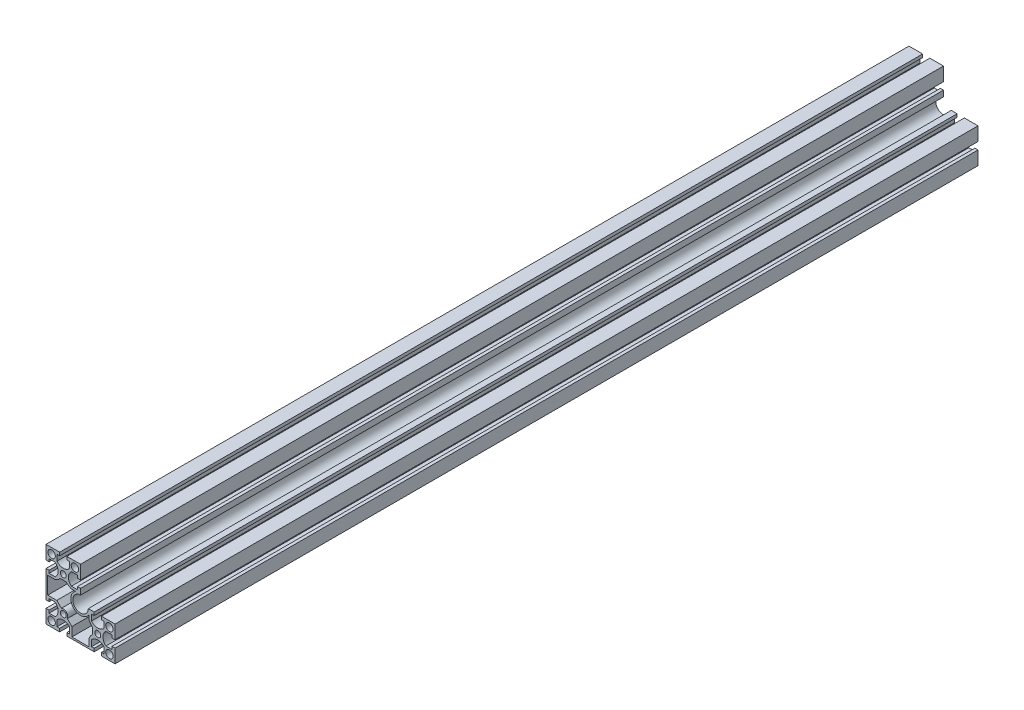
SolidWorks part; units mm, degrees
material "6063 T5"
ref_plane "Спереди" through (0, 0, 0) normal (0, 0, 1) x (1, 0, 0)
ref_plane "Сверху" through (0, 0, 0) normal (0, 1, 0) x (1, 0, 0)
ref_plane "Справа" through (0, 0, 0) normal (1, 0, 0) x (0, 0, -1)
sketch "Эскиз1" plane through (0, 0, 0) normal (0, 0, 1) x (1, 0, 0)
  line L0 (-19.9727, 74.2967) -> (60.0273, 74.2967) construction
  line L1 (0, 40) -> (0, 0) construction
  line L2 (0, 0) -> (40, 0) construction
  line L3 (-20, 47.3) -> (-20, 60)
  line L4 (-20, 60) -> (-7.3, 60)
  line L5 (7.3, 60) -> (20, 60)
  line L6 (20, 60) -> (20, 47.3)
  line L7 (0, 20) -> (-33.7669, 20) construction
  line L8 (-20, -7.3) -> (-20, -20)
  line L9 (-20, -20) -> (-7.3, -20)
  line L10 (-20, 32.7) -> (-20, 7.3)
  line L11 (0, 0) -> (36.7738, 36.7738) construction
  line L12 (32.7, -20) -> (7.3, -20)
  line L13 (47.3, -20) -> (60, -20)
  line L14 (60, -20) -> (60, -7.3)
  line L15 (60, 7.3) -> (60, 20)
  line L16 (60, 20) -> (47.3, 20)
  line L17 (20, 32.7) -> (20, 29)
  line L18 (29, 20) -> (32.7, 20)
  line L19 (-2.208, 4.708) -> (-7.5, 10)
  line L20 (-7.5, 10) -> (-18, 10)
  line L21 (-18, 10) -> (-18, 30)
  line L22 (-18, 30) -> (-9, 30)
  line L23 (-9, 30) -> (-5.451, 32.049)
  line L24 (-5.451, 32.049) -> (-3.5, 34)
  line L25 (-3.5, 34) -> (3.5, 34)
  line L26 (3.5, 34) -> (5.451, 32.049)
  line L27 (5.451, 32.049) -> (9, 30)
  line L28 (9, 30) -> (14.7379, 30)
  line L29 (30, 9) -> (30, 14.7379)
  line L30 (32.049, 5.451) -> (30, 9)
  line L31 (34, 3.5) -> (32.049, 5.451)
  line L32 (34, -3.5) -> (34, 3.5)
  line L33 (32.049, -5.451) -> (34, -3.5)
  line L34 (30, -9) -> (32.049, -5.451)
  line L35 (30, -18) -> (30, -9)
  line L36 (10, -18) -> (30, -18)
  line L37 (10, -7.5) -> (10, -18)
  line L38 (4.708, -2.208) -> (10, -7.5)
  circle A0 centre (0, 40) radius 3.4
  circle A1 centre (-13.5, 53.5) radius 4.3
  circle A3 centre (13.5, 53.5) radius 4.3
  circle A4 centre (-13.5, -13.5) radius 4.3
  circle A5 centre (0, 0) radius 3.4
  circle A6 centre (40, 0) radius 3.4
  circle A7 centre (53.5, 13.5) radius 4.3
  circle A8 centre (53.5, -13.5) radius 4.3
  arc A9 (20, 29) -> (29, 20) centre (20, 20) ccw
  arc A10 (4.708, -2.208) -> (-2.208, 4.708) centre (0, 0) ccw
  arc A11 (14.7379, 30) -> (30, 14.7379) centre (20, 20) ccw
  point P7 (-20, 40)
  point P11 (0, 40)
  point P62 (0, 34)
  line B0 (-20, 47.3) -> (-20, 44.2)
  line B1 (-20, 44.2) -> (-16.4, 44.2)
  line B2 (-16.4, 44.2) -> (-16.4, 47.3)
  line B3 (-16.4, 47.3) -> (-9.4, 47.3)
  line B4 (-9.4, 32.7) -> (-16.4, 32.7)
  line B5 (-16.4, 32.7) -> (-16.4, 35.8)
  line B6 (-16.4, 35.8) -> (-20, 35.8)
  line B7 (-20, 35.8) -> (-20, 32.7)
  line B8 (-20, 47.3) -> (-20, 32.7) construction
  arc B9 (-9.4, 47.3) -> (-9.4, 32.7) centre (-15.4795, 40) cw
  line B10 (7.3, 60) -> (4.2, 60)
  line B11 (4.2, 60) -> (4.2, 56.4)
  line B12 (4.2, 56.4) -> (7.3, 56.4)
  line B13 (7.3, 56.4) -> (7.3, 49.4)
  line B14 (-7.3, 49.4) -> (-7.3, 56.4)
  line B15 (-7.3, 56.4) -> (-4.2, 56.4)
  line B16 (-4.2, 56.4) -> (-4.2, 60)
  line B17 (-4.2, 60) -> (-7.3, 60)
  line B18 (7.3, 60) -> (-7.3, 60) construction
  arc B19 (7.3, 49.4) -> (-7.3, 49.4) centre (0, 55.4795) cw
  line B20 (20, 32.7) -> (20, 35.8)
  line B21 (20, 35.8) -> (16.4, 35.8)
  line B22 (16.4, 35.8) -> (16.4, 32.7)
  line B23 (16.4, 32.7) -> (9.4, 32.7)
  line B24 (9.4, 47.3) -> (16.4, 47.3)
  line B25 (16.4, 47.3) -> (16.4, 44.2)
  line B26 (16.4, 44.2) -> (20, 44.2)
  line B27 (20, 44.2) -> (20, 47.3)
  line B28 (20, 32.7) -> (20, 47.3) construction
  arc B29 (9.4, 32.7) -> (9.4, 47.3) centre (15.4795, 40) cw
  line B30 (-20, -7.3) -> (-20, -4.2)
  line B31 (-20, -4.2) -> (-16.4, -4.2)
  line B32 (-16.4, -4.2) -> (-16.4, -7.3)
  line B33 (-16.4, -7.3) -> (-9.4, -7.3)
  line B34 (-9.4, 7.3) -> (-16.4, 7.3)
  line B35 (-16.4, 7.3) -> (-16.4, 4.2)
  line B36 (-16.4, 4.2) -> (-20, 4.2)
  line B37 (-20, 4.2) -> (-20, 7.3)
  line B38 (-20, -7.3) -> (-20, 7.3) construction
  arc B39 (-9.4, -7.3) -> (-9.4, 7.3) centre (-15.4795, 0) ccw
  line B40 (7.3, -20) -> (4.2, -20)
  line B41 (4.2, -20) -> (4.2, -16.4)
  line B42 (4.2, -16.4) -> (7.3, -16.4)
  line B43 (7.3, -16.4) -> (7.3, -9.4)
  line B44 (-7.3, -9.4) -> (-7.3, -16.4)
  line B45 (-7.3, -16.4) -> (-4.2, -16.4)
  line B46 (-4.2, -16.4) -> (-4.2, -20)
  line B47 (-4.2, -20) -> (-7.3, -20)
  line B48 (7.3, -20) -> (-7.3, -20) construction
  arc B49 (7.3, -9.4) -> (-7.3, -9.4) centre (0, -15.4795) ccw
  line B50 (32.7, 20) -> (35.8, 20)
  line B51 (35.8, 20) -> (35.8, 16.4)
  line B52 (35.8, 16.4) -> (32.7, 16.4)
  line B53 (32.7, 16.4) -> (32.7, 9.4)
  line B54 (47.3, 9.4) -> (47.3, 16.4)
  line B55 (47.3, 16.4) -> (44.2, 16.4)
  line B56 (44.2, 16.4) -> (44.2, 20)
  line B57 (44.2, 20) -> (47.3, 20)
  line B58 (32.7, 20) -> (47.3, 20) construction
  arc B59 (32.7, 9.4) -> (47.3, 9.4) centre (40, 15.4795) ccw
  line B60 (60, 7.3) -> (60, 4.2)
  line B61 (60, 4.2) -> (56.4, 4.2)
  line B62 (56.4, 4.2) -> (56.4, 7.3)
  line B63 (56.4, 7.3) -> (49.4, 7.3)
  line B64 (49.4, -7.3) -> (56.4, -7.3)
  line B65 (56.4, -7.3) -> (56.4, -4.2)
  line B66 (56.4, -4.2) -> (60, -4.2)
  line B67 (60, -4.2) -> (60, -7.3)
  line B68 (60, 7.3) -> (60, -7.3) construction
  arc B69 (49.4, 7.3) -> (49.4, -7.3) centre (55.4795, 0) ccw
  line B70 (47.3, -20) -> (44.2, -20)
  line B71 (44.2, -20) -> (44.2, -16.4)
  line B72 (44.2, -16.4) -> (47.3, -16.4)
  line B73 (47.3, -16.4) -> (47.3, -9.4)
  line B74 (32.7, -9.4) -> (32.7, -16.4)
  line B75 (32.7, -16.4) -> (35.8, -16.4)
  line B76 (35.8, -16.4) -> (35.8, -20)
  line B77 (35.8, -20) -> (32.7, -20)
  line B78 (47.3, -20) -> (32.7, -20) construction
  arc B79 (47.3, -9.4) -> (32.7, -9.4) centre (40, -15.4795) ccw
  dimension "D3" = 6.8
  dimension "D6" = 8.6
  dimension "D7" = 6.5
  dimension "D10" = 9
  dimension "D11" = 11.3
  dimension "D22" = 5.2
  dimension "D1" = 80
  dimension "D2" = 40
  dimension "D4" = 20
  dimension "D8" = 6.5
  dimension "D9" = 45
  dimension "D12" = 2.7
  dimension "D13" = 2.7
  dimension "D14" = 7
  dimension "D15" = 45
  dimension "D16" = 6
  dimension "D17" = 30
  dimension "D18" = 2
  dimension "D19" = 9
  dimension "D20" = 2.7
  dimension "D21" = 10.5
  dimension "D5" = 3
sketch_block_instance "8G(14,5С)-1"
sketch_block "8G(14,5С)" parameters "D4"=6.5, "D1"=14.6, "D2"=8.4, "D3"=2.2, "D5"=6
sketch_block_instance "8G(14,5С)-3"
sketch_block_instance "8G(14,5С)-4"
sketch_block_instance "8G(14,5С)-5"
sketch_block_instance "8G(14,5С)-6"
sketch_block_instance "8G(14,5С)-7"
sketch_block_instance "8G(14,5С)-8"
sketch_block_instance "8G(14,5С)-9"
extrude "Бобышка-Вытянуть1" add sketch "Эскиз1" along normal blind 1000 contours B79 B73 B72 B71 B70 L13 L14 B67 B66 B65 B64 B69 B63 B62 B61 B60 L15 L16 B57 B56 B55 B54 B59 B53 B52 B51 B50 L18 A9 L17 B20 B21 B22 B23 B29 B24 B25 B26 B27 L6 L5 B10 B11 B12 B13 B19 B14 B15 B16 B17 L4
